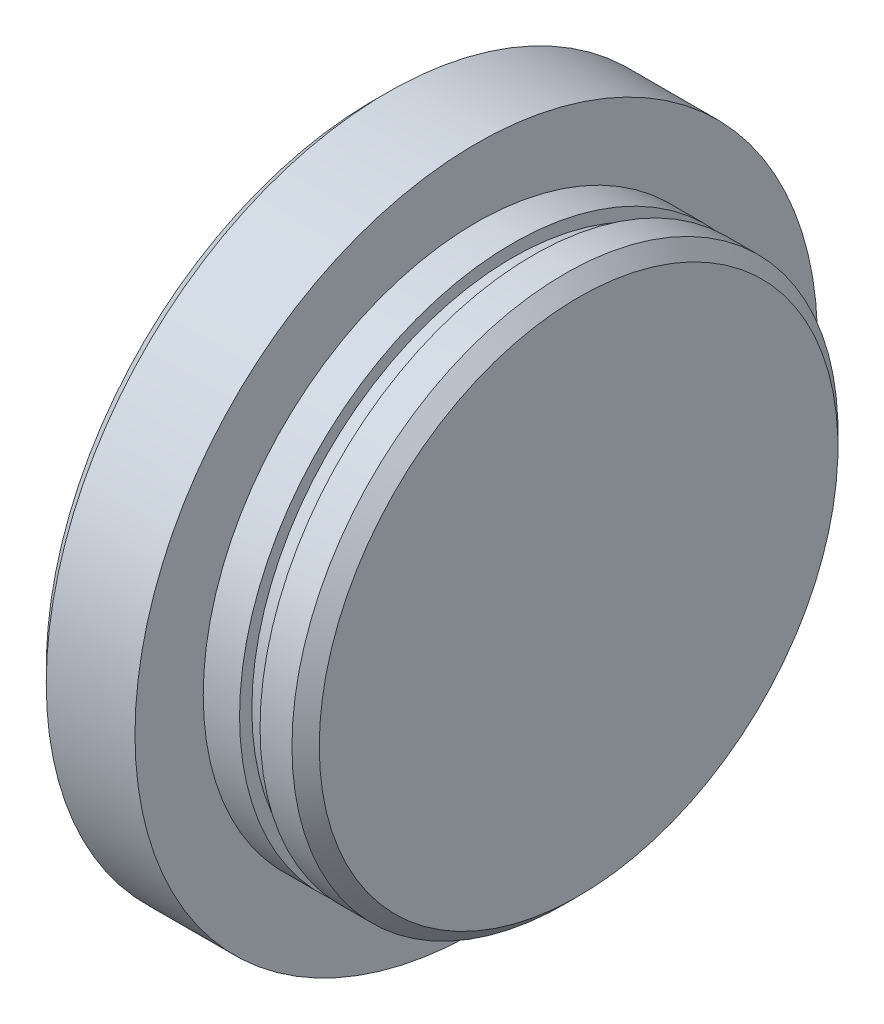
SolidWorks part; units mm, degrees
ref_plane "Ebene vorne" through (0, 0, 0) normal (0, 0, 1) x (1, 0, 0)
ref_plane "Ebene oben" through (0, 0, 0) normal (0, 1, 0) x (1, 0, 0)
ref_plane "Ebene rechts" through (0, 0, 0) normal (1, 0, 0) x (0, 0, -1)
sketch "Skizze1" plane through (0, 0, 0) normal (0, 0, 1) x (1, 0, 0)
  line L0 (0, 0) -> (85.6916, 0) construction
  line L1 (0, 0) -> (0, 50)
  line L2 (0, 50) -> (15, 50)
  line L3 (15, 50) -> (15, 40)
  line L4 (15, 40) -> (20.3221, 40)
  line L5 (30, 40) -> (30, 0)
  line L6 (0, 0) -> (30, 0)
  line L7 (20.3221, 40) -> (20.3221, 38.2)
  line L8 (20.3221, 38.2) -> (23.3221, 38.2)
  line L9 (23.3221, 38.2) -> (23.3221, 40)
  line L10 (23.3221, 40) -> (30, 40)
  dimension "D1" = 80
  dimension "D2" = 30
  dimension "D3" = 15
  dimension "D4" = 100
  dimension "D5" = 3
  dimension "D6" = 1.8
revolve "Rotation1" add sketch "Skizze1" angle 360 about L0
chamfer "Fase1" distance 2 angle 45 2 edges at (0, 0, 50) (30, 0, 40)
